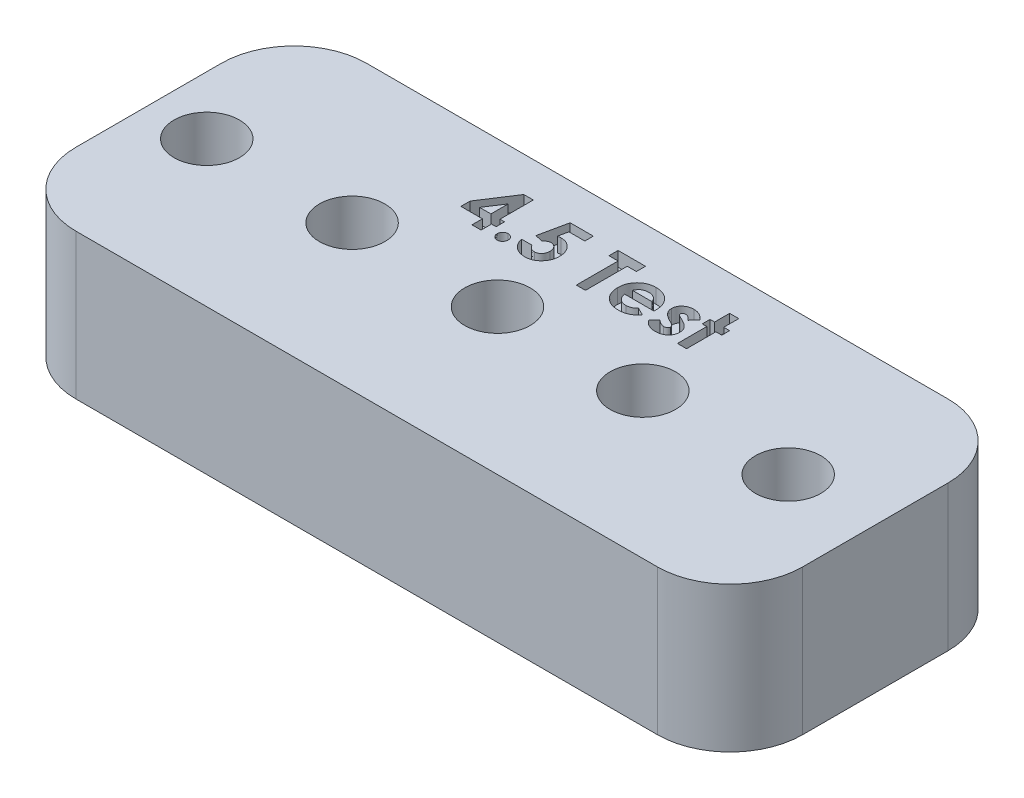
SolidWorks part; units mm, degrees
ref_plane "Front Plane" through (0, 0, 0) normal (0, 0, 1) x (1, 0, 0)
ref_plane "Top Plane" through (0, 0, 0) normal (0, 1, 0) x (1, 0, 0)
ref_plane "Right Plane" through (0, 0, 0) normal (1, 0, 0) x (0, 0, -1)
sketch "Sketch1" plane through (0, 0, 0) normal (0, 1, 0) x (1, 0, 0)
  line L1 (-50, 10) -> (50, 10)
  line L2 (-50, 10) -> (-50, -10)
  line L3 (-50, -10) -> (50, -10)
  line L4 (50, 10) -> (50, -10)
  line L5 (-50, 10) -> (50, -10) construction
  line L6 (-50, -10) -> (50, 10) construction
  point P0 (0, 0)
  dimension "D1" = 100
  dimension "D2" = 20
extrude "Boss-Extrude1" add sketch "Sketch1" along normal blind 10
sketch "Sketch2" plane through (0, 10, 0) normal (0, 1, 0) x (1, 0, 0)
  line L0 (0, 10) -> (0, -10) construction
  line L1 (50, 10) -> (-50, 10) construction
  line L2 (-50, -10) -> (50, -10) construction
  line L3 (-50, 0) -> (50, 0) construction
  line L4 (-50, 10) -> (-50, -10) construction
  line L5 (50, -10) -> (50, 10) construction
  point P12 (-6, 0)
  point P13 (-16, 0)
  point P14 (46, 0)
  point P15 (-26, 0)
  point P16 (-36, 0)
  point P17 (-46, 0)
  point P18 (36, 0)
  point P19 (26, 0)
  point P20 (16, 0)
  point P21 (6, 0)
  dimension "D1" = 6
  dimension "D2" = 5
hole_wizard "M4 Clearance Hole1" positions "Sketch34" profile "Sketch4" hole size "M4" standard "ANSI Metric"
sketch "Sketch34" plane through (0, 10, 0) normal (0, 1, 0) x (1, 0, 0)
  point P0 (-6, 0)
  point P3 (-16, 0)
sketch "Sketch4" plane through (-6, 10, 0) normal (1, 0, 0) x (0, 0, 1)
  line L0 (0, 0) -> (0, 6.3519)
  line L1 (0, 6.3519) -> (2.25, 5)
  line L2 (2.25, 5) -> (2.25, 0)
  line L5 (2.25, 0) -> (0, 0)
  line L10 (0, 6.3519) -> (-2.25, 5) construction
  line L11 (0, -6.35) -> (0, 107.95) construction
  dimension "Hole Dia." = 4.5
  dimension "Hole Depth" = 5
  dimension "Drill Angle" = 118
hole_wizard "M4 Clearance Hole2" positions "Sketch35" profile "Sketch7" hole size "M4" standard "ANSI Metric"
sketch "Sketch35" plane through (0, 10, 0) normal (0, 1, 0) x (1, 0, 0)
  point P0 (-26, 0)
  point P3 (-36, 0)
sketch "Sketch7" plane through (-26, 10, 0) normal (1, 0, 0) x (0, 0, 1)
  line L0 (0, 0) -> (0, 6.3519)
  line L1 (0, 6.3519) -> (2.25, 5)
  line L2 (2.25, 5) -> (2.25, 0)
  line L5 (2.25, 0) -> (0, 0)
  line L10 (0, 6.3519) -> (-2.25, 5) construction
  line L11 (0, -6.35) -> (0, 107.95) construction
  dimension "Hole Dia." = 4.5
  dimension "Hole Depth" = 5
  dimension "Drill Angle" = 118
sketch "Sketch9" plane through (0, 10, 0) normal (0, 1, 0) x (1, 0, 0)
  line L0 (-50, 4) -> (0, 4) construction
  line L1 (-50, 10) -> (-50, -10) construction
  line L3 (50, 10) -> (-50, 10) construction
  line L4 (0, 10) -> (0, -10) construction
  text T0 "<b>4.5 Test</b>\r\n" font "Century Gothic" height 3.5
  dimension "D1" = 6
extrude "Cut-Extrude1" cut sketch "Sketch9" against normal blind 1
hole_wizard "M4 Clearance Hole3" positions "Sketch36" profile "Sketch11" hole size "M4" standard "ANSI Metric"
sketch "Sketch36" plane through (0, 10, 0) normal (0, 1, 0) x (1, 0, 0)
  point P0 (-46, 0)
sketch "Sketch11" plane through (-46, 10, 0) normal (1, 0, 0) x (0, 0, 1)
  line L0 (0, 0) -> (0, 6.3519)
  line L1 (0, 6.3519) -> (2.25, 5)
  line L2 (2.25, 5) -> (2.25, 0)
  line L5 (2.25, 0) -> (0, 0)
  line L10 (0, 6.3519) -> (-2.25, 5) construction
  line L11 (0, -6.35) -> (0, 107.95) construction
  dimension "Hole Dia." = 4.5
  dimension "Hole Depth" = 5
  dimension "Drill Angle" = 118
hole_wizard "Ø5.0 (5) Diameter Hole1" positions "Sketch29" profile "Sketch15" hole size "Ø5.0" standard "ANSI Metric"
sketch "Sketch29" plane through (0, 10, 0) normal (0, 1, 0) x (1, 0, 0)
  point P0 (6, 0)
  point P3 (16, 0)
sketch "Sketch15" plane through (6, 10, 0) normal (1, 0, 0) x (0, 0, 1)
  line L0 (0, 0) -> (0, 6.5022)
  line L1 (0, 6.5022) -> (2.5, 5)
  line L2 (2.5, 5) -> (2.5, 0)
  line L5 (2.5, 0) -> (0, 0)
  line L10 (0, 6.5022) -> (-2.5, 5) construction
  line L11 (0, -6.35) -> (0, 107.95) construction
  dimension "Hole Dia." = 5
  dimension "Hole Depth" = 5
  dimension "Drill Angle" = 118
hole_wizard "Ø5.1 (5.1) Diameter Hole1" positions "Sketch30" profile "Sketch18" hole size "Ø5.1" standard "ANSI Metric"
sketch "Sketch30" plane through (0, 10, 0) normal (0, 1, 0) x (1, 0, 0)
  point P0 (26, 0)
  point P3 (36, 0)
sketch "Sketch18" plane through (26, 10, 0) normal (1, 0, 0) x (0, 0, 1)
  line L0 (0, 0) -> (0, 6.5322)
  line L1 (0, 6.5322) -> (2.55, 5)
  line L2 (2.55, 5) -> (2.55, 0)
  line L5 (2.55, 0) -> (0, 0)
  line L10 (0, 6.5322) -> (-2.55, 5) construction
  line L11 (0, -6.35) -> (0, 107.95) construction
  dimension "Hole Dia." = 5.1
  dimension "Hole Depth" = 5
  dimension "Drill Angle" = 118
hole_wizard "Ø5.2 (5.2) Diameter Hole1" positions "Sketch32" profile "Sketch21" hole size "Ø5.2" standard "ANSI Metric"
sketch "Sketch32" plane through (0, 10, 0) normal (0, 1, 0) x (1, 0, 0)
  point P0 (46, 0)
sketch "Sketch21" plane through (46, 10, 0) normal (1, 0, 0) x (0, 0, 1)
  line L0 (0, 0) -> (0, 6.5622)
  line L1 (0, 6.5622) -> (2.6, 5)
  line L2 (2.6, 5) -> (2.6, 0)
  line L5 (2.6, 0) -> (0, 0)
  line L10 (0, 6.5622) -> (-2.6, 5) construction
  line L11 (0, -6.35) -> (0, 107.95) construction
  dimension "Hole Dia." = 5.2
  dimension "Hole Depth" = 5
  dimension "Drill Angle" = 118
sketch "Sketch24" plane through (0, 10, 0) normal (0, 1, 0) x (1, 0, 0)
  line L0 (0, 4) -> (50, 4) construction
  line L1 (0, 10) -> (0, -10) construction
  line L2 (50, -10) -> (50, 10) construction
  line L3 (50, 10) -> (-50, 10) construction
  text T0 "<b>M3 Area</b>" font "Century Gothic" height 3.5
  dimension "D1" = 6
extrude "Cut-Extrude2" cut sketch "Sketch24" against normal blind 1
sketch "Sketch25"
  dimension "D1" = 3
  dimension "D2" = 5.5
  dimension "D3" = 2
fillet "Fillet1" radius 5 4 edges at (50, 5, -10) (50, 5, 10) (-50, 5, -10) (-50, 5, 10)
sketch "Sketch33" plane through (0, 0, 0) normal (0, 1, 0) x (1, 0, 0)
  line L0 (50, -5) -> (50, 5) construction
  line L1 (0, 10) -> (50, 10)
  line L2 (0, 10) -> (0, -11.0309)
  line L3 (0, -11.0309) -> (50, -11.0309)
  line L4 (50, 10) -> (50, -11.0309)
  point P7 (0, 0)
extrude "Cut-Extrude4" cut sketch "Sketch33" along normal through all
fillet "Fillet2" radius 5 2 edges at (0, 5, 10) (0, 5, -10)
